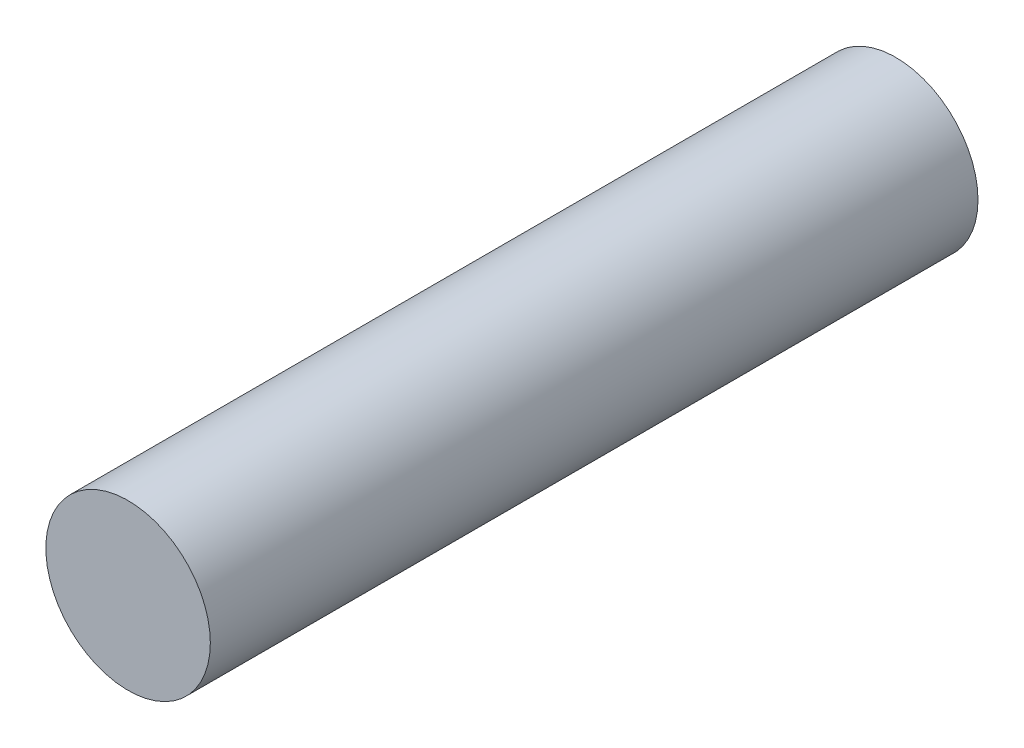
SolidWorks part; units mm, degrees
ref_plane "Front Plane" through (0, 0, 0) normal (0, 0, 1) x (1, 0, 0)
ref_plane "Top Plane" through (0, 0, 0) normal (0, 1, 0) x (1, 0, 0)
ref_plane "Right Plane" through (0, 0, 0) normal (1, 0, 0) x (0, 0, -1)
sketch "Sketch1" plane through (0, 0, 0) normal (0, 0, 1) x (1, 0, 0)
  circle A0 centre (0, 0) radius 4.7625
  dimension "D1" = 9.525
extrude "Boss-Extrude1" add sketch "Sketch1" along normal blind 44.45
